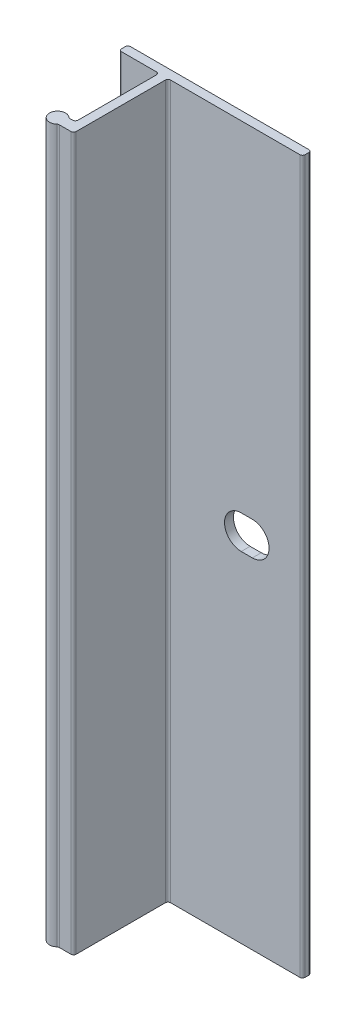
SolidWorks part; units mm, degrees
material "6463-T6"
ref_plane "Front Plane" through (0, 0, 0) normal (0, 0, 1) x (1, 0, 0)
ref_plane "Top Plane" through (0, 0, 0) normal (0, 1, 0) x (1, 0, 0)
ref_plane "Right Plane" through (0, 0, 0) normal (1, 0, 0) x (0, 0, -1)
sketch "Sketch2" plane through (0, 0, 0) normal (0, 1, 0) x (1, 0, 0)
  line L0 (0, -3.4226) -> (0, 3.4226) construction
  line L16 (-5.334, 0) -> (20.066, 0)
  line L18 (20.447, -0.381) -> (20.447, -0.889)
  line L19 (20.066, -1.27) -> (1.651, -1.27)
  line L20 (1.27, -1.651) -> (1.27, -14.351)
  line L52 (0, -1.651) -> (0, -12.827)
  line L53 (-55, 0) -> (55, 0) construction
  line L54 (-0.77, -13.208) -> (-0.381, -13.208)
  line L55 (-0.77, -14.732) -> (0.889, -14.732)
  line L57 (-0.381, -1.27) -> (-5.334, -1.27)
  line L58 (-5.715, -0.889) -> (-5.715, -0.381)
  arc A11 (20.066, 0) -> (20.447, -0.381) centre (20.066, -0.381) cw
  arc A12 (20.447, -0.889) -> (20.066, -1.27) centre (20.066, -0.889) cw
  arc A19 (1.651, -1.27) -> (1.27, -1.651) centre (1.651, -1.651) ccw
  arc A20 (-1.022, -13.1128) -> (-1.022, -14.8273) centre (-1.778, -13.97) ccw
  arc A23 (0, -12.827) -> (-0.381, -13.208) centre (-0.381, -12.827) cw
  arc A26 (-0.77, -14.732) -> (-1.022, -14.8273) centre (-0.77, -15.113) ccw
  arc A27 (-0.77, -13.208) -> (-1.022, -13.1128) centre (-0.77, -12.827) cw
  arc A28 (-5.715, -0.381) -> (-5.334, 0) centre (-5.334, -0.381) cw
  arc A29 (-5.334, -1.27) -> (-5.715, -0.889) centre (-5.334, -0.889) cw
  arc A30 (-0.381, -1.27) -> (0, -1.651) centre (-0.381, -1.651) cw
  arc A31 (0.889, -14.732) -> (1.27, -14.351) centre (0.889, -14.351) ccw
  dimension "D1" = 26.162
  dimension "D7" = 13.97
  dimension "D6" = 14.732
  dimension "D10" = 1.524
  dimension "D9" = 1.778
  dimension "D3" = 0.381
  dimension "D8" = 1.143
  dimension "D2" = 1.27
  dimension "D4" = 5.715
  dimension "D5" = 1.27
extrude "Boss-Extrude1" add sketch "Sketch2" along normal mid plane 101.6
sketch "Sketch3" plane through (0, 0, 1.27) normal (0, 0, 1) x (1, 0, 0)
  line L0 (11.7157, 0) -> (13.3033, 0) construction
  line L1 (11.7157, 2.3813) -> (13.3032, 2.3813)
  line L2 (11.7157, -2.3813) -> (13.3032, -2.3812)
  line L3 (20.447, 50.8) -> (20.447, -50.8) construction
  arc A0 (11.7157, 2.3813) -> (11.7157, -2.3813) centre (11.7157, 0) ccw
  arc A1 (13.3032, -2.3812) -> (13.3032, 2.3813) centre (13.3033, 0) ccw
  point P3 (12.5095, 0)
  dimension "D1" = 4.7625
  dimension "D2" = 6.35
  dimension "D3" = 7.9375
extrude "Cut-Extrude1" cut sketch "Sketch3" against normal through all
